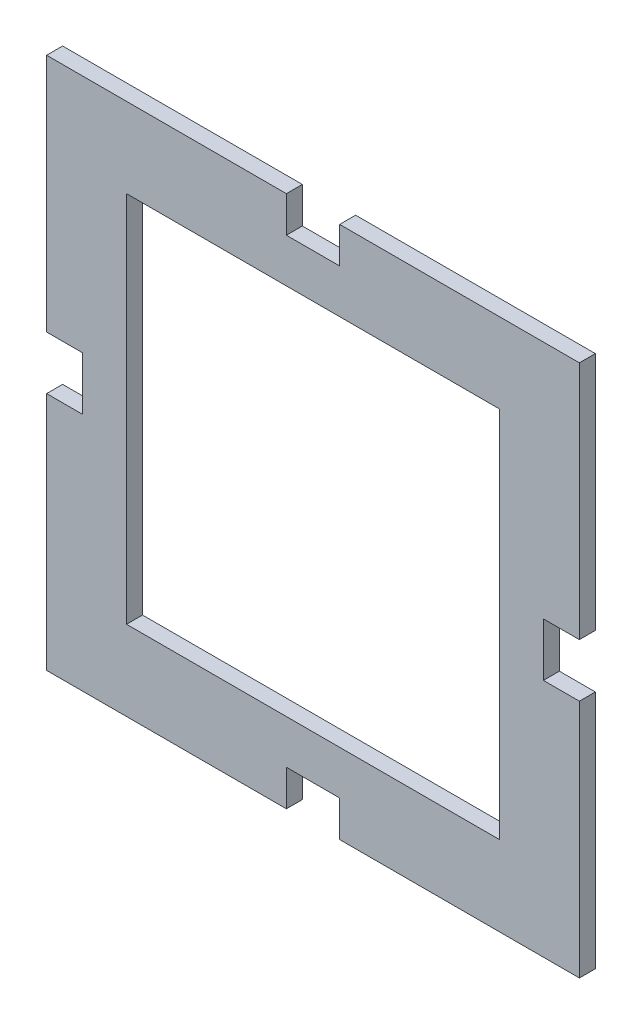
SolidWorks part; units mm, degrees
ref_plane "Front Plane" through (0, 0, 0) normal (0, 0, 1) x (1, 0, 0)
ref_plane "Top Plane" through (0, 0, 0) normal (0, 1, 0) x (1, 0, 0)
ref_plane "Right Plane" through (0, 0, 0) normal (1, 0, 0) x (0, 0, -1)
sketch "Sketch1" plane through (0, 0, 0) normal (0, 0, 1) x (1, 0, 0)
  line L0 (-50, 50) -> (50, -50) construction
  line L1 (-50, 50) -> (50, 50)
  line L2 (-50, 50) -> (-50, -50)
  line L3 (-50, -50) -> (50, -50)
  line L4 (50, 50) -> (50, -50)
  line L6 (50, 50) -> (0, 0) construction
  line L7 (0, 0) -> (-50, -50) construction
  line L8 (-35, -35) -> (35, -35)
  line L9 (35, 35) -> (35, -35)
  line L10 (-35, 35) -> (35, 35)
  line L11 (-35, 35) -> (-35, -35)
  line L12 (-43.24, 50) -> (-43.24, -50) construction
  line L13 (-50, 43.24) -> (50, 43.24) construction
  line L14 (-5, -50) -> (-5, -43.24)
  line L15 (-5, 50) -> (5, 50)
  line L16 (-5, 50) -> (-5, 43.24)
  line L17 (-5, 43.24) -> (5, 43.24)
  line L18 (5, 50) -> (5, 43.24)
  line L19 (-50, 5) -> (-43.24, 5)
  line L20 (-50, 5) -> (-50, -5)
  line L21 (-50, -5) -> (-43.24, -5)
  line L22 (-43.24, 5) -> (-43.24, -5)
  line L23 (5, -50) -> (5, -43.24)
  line L24 (5, -43.24) -> (-5, -43.24)
  line L25 (50, 5) -> (43.24, 5)
  line L26 (43.24, -5) -> (43.24, 5)
  line L27 (50, -5) -> (43.24, -5)
  dimension "D1" = 100
  dimension "D2" = 15
  dimension "D3" = 6.76
  dimension "D4" = 6.76
  dimension "D5" = 10
  dimension "D6" = 5
  dimension "D7" = 5
extrude "Boss-Extrude1" add sketch "Sketch1" along normal blind 3 contours L4 L27 L26 L25 L1 L18 L17 L16 L2 L19 L22 L21 L3 L14 L24 L23 L11 L10 L9 L8
